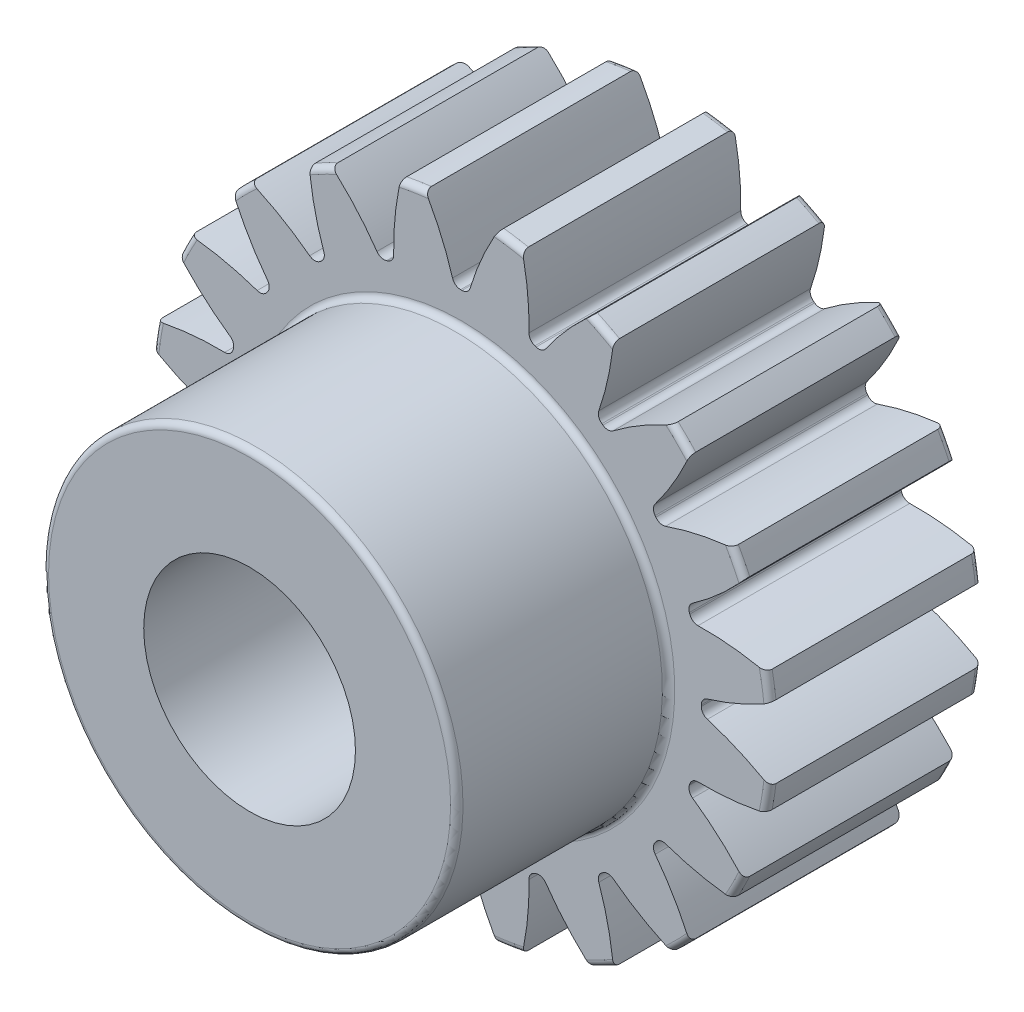
SolidWorks part; units mm, degrees
ref_plane "Front Plane" through (0, 0, 0) normal (0, 0, 1) x (1, 0, 0)
ref_plane "Top Plane" through (0, 0, 0) normal (0, 1, 0) x (1, 0, 0)
ref_plane "Right Plane" through (0, 0, 0) normal (1, 0, 0) x (0, 0, -1)
sketch "Sketch1" plane through (0, 0, 0) normal (0, 0, 1) x (1, 0, 0)
  line L0 (-254, 0) -> (254, 0) construction
  circle A0 centre (0, 0) radius 13.97 construction
  circle A1 centre (0, 0) radius 12.7 construction
  circle A2 centre (0, 0) radius 10.795 construction
  circle A3 centre (0, 0) radius 9.3218 construction
  circle A4 centre (0, 0) radius 4.7625 construction
  dimension "D2" = 1.27
  dimension "D3" = 3.175
  dimension "D1" = 3.175
sketch "Sketch2" plane through (0, 0, 0) normal (1, 0, 0) x (0, 0, -1)
  line L0 (0, 0) -> (-9.525, 0) construction
  line L1 (-9.525, 0) -> (-19.05, 0) construction
  dimension "Overall Width" = 19.05
  dimension "Face Width" = 9.525
sketch "Sketch4" plane through (0, 0, 0) normal (1, 0, 0) x (0, 0, -1)
  line L0 (-19.05, 4.7625) -> (-19.05, 9.3218)
  line L1 (-19.05, 9.3218) -> (-9.525, 9.3218)
  line L2 (-9.525, 9.3218) -> (-9.525, 13.97)
  line L3 (-9.525, 13.97) -> (0, 13.97)
  line L4 (0, 13.97) -> (0, 4.7625)
  line L5 (-9.525, 9.3218) -> (-9.525, 0) construction
  line L6 (0, 13.97) -> (0, -13.97) construction
  line L7 (-9.525, 9.3218) -> (0, 9.3218) construction
  line L12 (-19.05, 4.7625) -> (0, 4.7625)
revolve "Revolve1" add sketch "Sketch4" angle 360 about L1
fillet "Fillet2" radius 0.2794 4 edges at (0, 9.3218, 19.05) (0, 9.3218, 9.525) (0, 13.97, 9.525) (0, 13.97, 0)
sketch "Sketch7" plane through (0, 0, 9.525) normal (0, 0, 1) x (1, 0, 0)
  line L0 (0, 0) -> (0, 13.97) construction
  line L1 (0.9964, 12.6609) -> (1.5536, 13.8833) construction
  line L3 (2.1854, 13.798) -> (1.9867, 12.5436) construction
  line L4 (1.9867, 12.5436) -> (1.6887, 10.6621) construction
  line L5 (0, 0) -> (1.6887, 10.6621) construction
  line L6 (0.9964, 12.6609) -> (0, 0) construction
  line L7 (0.9964, 12.6609) -> (1.0961, 13.9269) construction
  line L8 (0.9964, 12.6609) -> (0, 0) construction
  circle A0 centre (0, 0) radius 13.97 construction
  arc A1 (-0.0294, 10.795) -> (0.0294, 10.795) centre (0, 0) cw
  circle A2 centre (0, 0) radius 10.795 construction
  arc A3 (-0.9964, 12.6609) -> (0.9964, 12.6609) centre (0, 0) cw construction
  circle A4 centre (0, 0) radius 12.7 construction
  arc A5 (2.7366, 13.6993) -> (1.6307, 13.8745) centre (0, 0) ccw construction
  arc A6 (0.9964, 12.6609) -> (2.9648, 12.3491) centre (0, 0) cw construction
  arc A7 (-1.6307, 13.8745) -> (1.6307, 13.8745) centre (0, 0) cw
  arc A8 (0.3952, 11.0658) -> (1.6307, 13.8745) centre (12.5529, 7.3942) cw
  arc A9 (-0.3952, 11.0658) -> (-1.6307, 13.8745) centre (-12.5529, 7.3942) ccw
  arc A10 (-0.0294, 10.795) -> (-0.3952, 11.0658) centre (-0.0305, 11.176) cw
  arc A11 (0.0294, 10.795) -> (0.3952, 11.0658) centre (0.0305, 11.176) ccw
  point P26 (-0.3154, 10.7904)
  point P29 (0.3154, 10.7904)
  dimension "D4" = 0.381
  dimension "D5" = 12.7
  dimension "D3" = 20
  dimension "D1" = 3.9898
  dimension "D2" = 1.9949
extrude "Cut-Extrude2" cut sketch "Sketch7" against normal through all
pattern_circular "CirPattern1" count 20 over 360 about axis through (0, 0, 0) along (0, 0, 1) of "Cut-Extrude2"
equation "\"D1@Sketch1\"=2.5*(\"Pitch Dia.@Sketch1\"/\"Number of Teeth@Sketch1\")"
equation "\"D1@CirPattern1\"=\"Number of Teeth@Sketch1\""
equation "\"D1@Fillet2\"=\"OD@Sketch1\"*.01"
equation "\"D1@Sketch7\"=3.14159*(\"Pitch Dia.@Sketch1\"/\"Number of Teeth@Sketch1\")"
equation "\"D2@Sketch7\"=\"D1@Sketch7\"/2"
equation "\"D4@Sketch7\"=\"D1@Sketch7\"*.0955"
equation "\"D5@Sketch7\"=\"Pitch Dia.@Sketch1\"/2"
